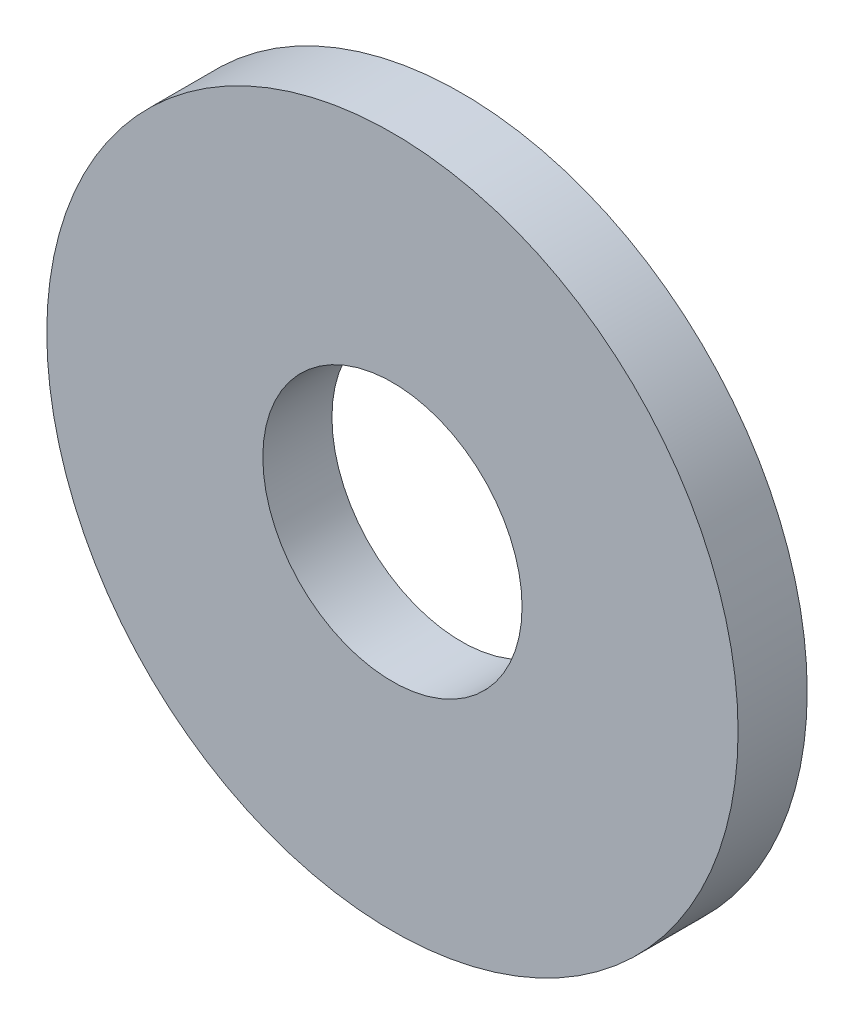
SolidWorks part; units mm, degrees
ref_plane "Plan de face" through (0, 0, 0) normal (0, 0, 1) x (1, 0, 0)
ref_plane "Plan de dessus" through (0, 0, 0) normal (0, 1, 0) x (1, 0, 0)
ref_plane "Plan de droite" through (0, 0, 0) normal (1, 0, 0) x (0, 0, -1)
sketch "Esquisse1" plane through (0, 0, 0) normal (0, 0, 1) x (1, 0, 0)
  circle A0 centre (0, 0) radius 4
  circle A1 centre (0, 0) radius 1.5
  dimension "D1" = 8
  dimension "D2" = 3
extrude "Boss.-Extru.1" add sketch "Esquisse1" along normal blind 0.8
